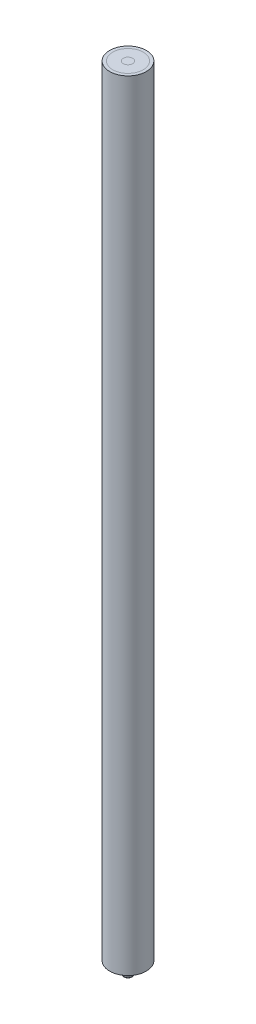
SolidWorks part; units mm, degrees
material "C110 COPPER"
ref_plane "Front Plane" through (0, 0, 0) normal (0, 0, 1) x (1, 0, 0)
ref_plane "Top Plane" through (0, 0, 0) normal (0, 1, 0) x (1, 0, 0)
ref_plane "Right Plane" through (0, 0, 0) normal (1, 0, 0) x (0, 0, -1)
sketch "Sketch1" plane through (0, 0, 0) normal (0, 1, 0) x (1, 0, 0)
  circle A0 centre (0, 0) radius 0.4597
  dimension "D1" = 0.9195
extrude "Boss-Extrude1" add sketch "Sketch1" along normal blind 76.2 and the other way blind 1.27
sketch "Sketch2" plane through (0, 0, 0) normal (0, 1, 0) x (1, 0, 0)
  circle A0 centre (0, 0) radius 1.4922
  circle A1 centre (0, 0) radius 0.4597 construction
  circle A2 centre (0, 0) radius 0.4597
  dimension "D1" = 2.9845
extrude "Boss-Extrude2" add sketch "Sketch2" along normal blind 76.2 separate body
sketch "Sketch3" plane through (0, 0, 0) normal (0, 1, 0) x (1, 0, 0)
  circle A0 centre (0, 0) radius 1.4922 construction
  circle A1 centre (0, 0) radius 1.4922
  circle A2 centre (0, 0) radius 1.7907
  dimension "D1" = 3.5814
extrude "Boss-Extrude3" add sketch "Sketch3" along normal blind 76.2 separate body
fillet "Fillet1" radius 0.254 1 edges at (0, -1.27, 0.4597)
